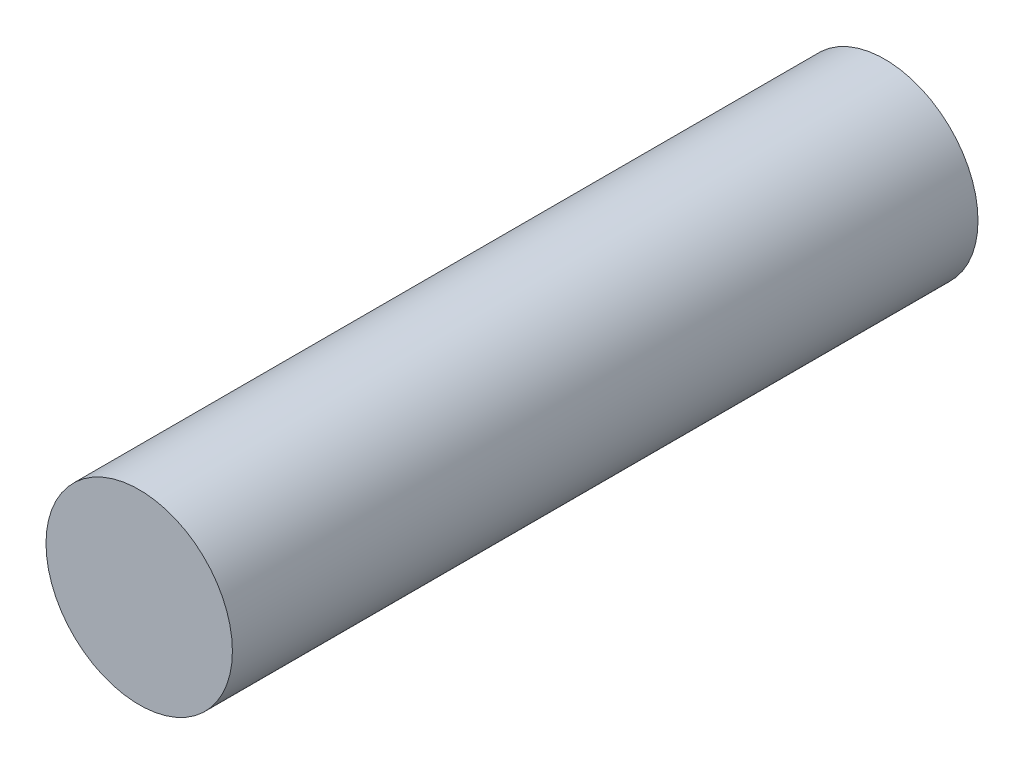
SolidWorks part; units mm, degrees
ref_plane "Front Plane" through (0, 0, 0) normal (0, 0, 1) x (1, 0, 0)
ref_plane "Top Plane" through (0, 0, 0) normal (0, 1, 0) x (1, 0, 0)
ref_plane "Right Plane" through (0, 0, 0) normal (1, 0, 0) x (0, 0, -1)
sketch "Sketch1" plane through (0, 0, 0) normal (0, 0, 1) x (1, 0, 0)
  circle A0 centre (0, 0) radius 6.35
extrude "Boss-Extrude1" add sketch "Sketch1" along normal blind 50.8
